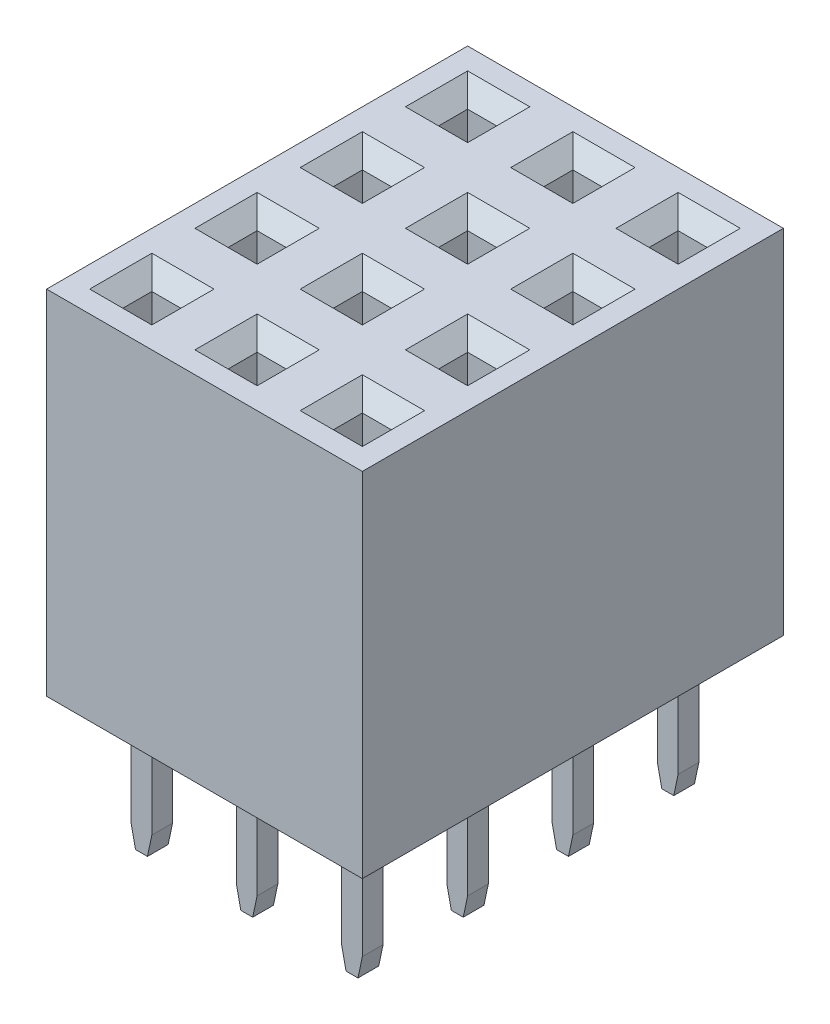
SolidWorks part; units mm, degrees
ref_plane "Спереди" through (0, 0, 0) normal (0, 0, 1) x (1, 0, 0)
ref_plane "Сверху" through (0, 0, 0) normal (0, 1, 0) x (1, 0, 0)
ref_plane "Справа" through (0, 0, 0) normal (1, 0, 0) x (0, 0, -1)
ref_plane "Плоскость1" through (0, 0, 0) normal (0, 1, 0) x (-1, 0, 0)
sketch "Эскиз1" plane through (0, 0, 0) normal (0, 1, 0) x (-1, 0, 0)
  line L0 (0, 0) -> (-5.5295, 0) construction
  line L1 (0, 0) -> (0, -2.1715) construction
  line L2 (-1.27, 1.27) -> (1.27, 1.27)
  line L3 (-1.27, 1.27) -> (-1.27, -1.27)
  line L4 (-1.27, -1.27) -> (1.27, -1.27)
  line L5 (1.27, 1.27) -> (1.27, -1.27)
  point P0 (-1.27, 1.27)
  point P1 (1.27, -1.27)
  point P2 (-1.27, -1.27)
  point P3 (1.27, 1.27)
  dimension "D1" = 2.54
  dimension "D6" = 1.27
extrude "Бобышка-Вытянуть1" add sketch "Эскиз1" along normal blind 8.51
sketch "Эскиз4" plane through (0, 8.51, 0) normal (0, 1, 0) x (1, 0, 0)
  line L0 (0, 0) -> (0.806, 0) construction
  line L1 (0, 0) -> (0, 1.2961) construction
  line L3 (-0.35, 0.35) -> (0.35, 0.35)
  line L4 (-0.35, 0.35) -> (-0.35, -0.35)
  line L5 (-0.35, -0.35) -> (0.35, -0.35)
  line L6 (0.35, 0.35) -> (0.35, -0.35)
  dimension "D1" = 0.7
extrude "Вырез-Вытянуть1" cut sketch "Эскиз4" against normal blind 8.21
chamfer "Фаска3" distance 0.4 angle 45 4 edges at (0.35, 8.51, 0) (0, 8.51, -0.35) (0, 8.51, 0.35) (-0.35, 8.51, 0)
sketch "Эскиз2" plane through (0, 0, 0) normal (0, 1, 0) x (-1, 0, 0)
  line L0 (0, 0) -> (0, -0.4454) construction
  line L1 (0.25, 0.25) -> (-0.25, 0.25)
  line L2 (0.25, 0.25) -> (0.25, -0.25)
  line L3 (0.25, -0.25) -> (-0.25, -0.25)
  line L4 (-0.25, 0.25) -> (-0.25, -0.25)
  line L5 (0, 0) -> (-0.4704, 0) construction
  dimension "D1" = 0.5
  dimension "D2" = 0.5
extrude "Бобышка-Вытянуть2" add sketch "Эскиз2" against normal blind 3.15
chamfer "Фаска2" distance 0.5 angle 12 2 edges at (0.25, -3.15, 0) (-0.25, -3.15, 0)
pattern_linear "Линейный массив1" count 4 spacing 2.54 along (0, 0, -1) count 3 spacing 2.54 along (-1, 0, 0) of "Бобышка-Вытянуть1", "Вырез-Вытянуть1", "Фаска3", "Бобышка-Вытянуть2", "Фаска2"
equation "\"D6@Эскиз1\"=2.54/2"
